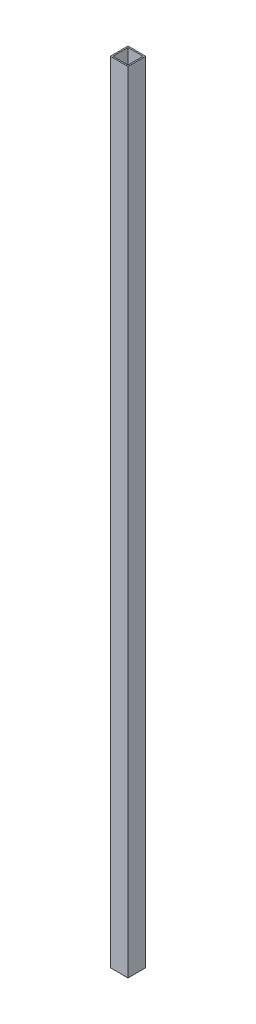
SolidWorks part; units mm, degrees
material "6063-T6"
ref_plane "Front Plane" through (0, 0, 0) normal (0, 0, 1) x (1, 0, 0)
ref_plane "Top Plane" through (0, 0, 0) normal (0, 1, 0) x (1, 0, 0)
ref_plane "Right Plane" through (0, 0, 0) normal (1, 0, 0) x (0, 0, -1)
sketch "Sketch1" plane through (0, 0, 0) normal (0, 1, 0) x (1, 0, 0)
  line L0 (41.275, 3.175) -> (41.275, 41.275)
  line L1 (0, 0) -> (44.45, 0)
  line L2 (0, 0) -> (0, 44.45)
  line L3 (0, 44.45) -> (44.45, 44.45)
  line L4 (44.45, 0) -> (44.45, 44.45)
  line L5 (3.175, 41.275) -> (41.275, 41.275)
  line L6 (3.175, 3.175) -> (3.175, 41.275)
  line L7 (3.175, 3.175) -> (41.275, 3.175)
  dimension "D1" = 44.45
  dimension "D2" = 3.175
extrude "Boss-Extrude1" add sketch "Sketch1" along normal blind 1981.2
sketch "Sketch2" plane through (0, 0, 0) normal (0, 0, 1) x (1, 0, 0)
  line L0 (0, 0) -> (44.45, 0) construction
  line L1 (44.45, 1981.2) -> (44.45, 0) construction
  circle A0 centre (22.225, 22.225) radius 18.2562
  circle A1 centre (22.225, 911.225) radius 18.2563
  dimension "D1" = 889
  dimension "D4" = 36.5125
  dimension "D2" = 22.225
  dimension "D3" = 22.225
extrude "Cut-Extrude1" [suppressed] cut sketch "Sketch2" against normal through all
sketch "Sketch3" plane through (44.45, 0, 0) normal (1, 0, 0) x (0, 0, -1)
  line L0 (44.45, 1981.2) -> (44.45, 0) construction
  line L1 (0, 0) -> (44.45, 0) construction
  circle A0 centre (22.225, 22.225) radius 4.7625
  circle A1 centre (22.225, 911.225) radius 4.7625
  dimension "D1" = 889
  dimension "D4" = 9.525
  dimension "D2" = 22.225
  dimension "D3" = 22.225
extrude "Cut-Extrude2" [suppressed] cut sketch "Sketch3" against normal through all
